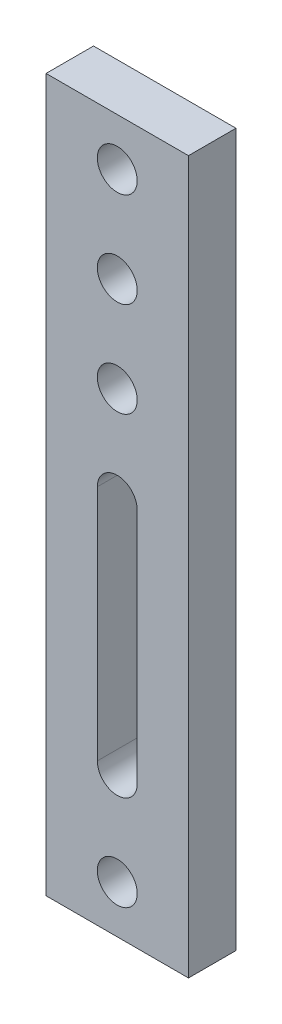
SolidWorks part; units mm, degrees
material "Простая углеродистая сталь"
ref_plane "Спереди" through (0, 0, 0) normal (0, 0, 1) x (1, 0, 0)
ref_plane "Сверху" through (0, 0, 0) normal (0, 1, 0) x (1, 0, 0)
ref_plane "Справа" through (0, 0, 0) normal (1, 0, 0) x (0, 0, -1)
sketch "Эскиз1" plane through (0, 0, 0) normal (0, 0, 1) x (1, 0, 0)
  line L1 (0, 0) -> (75, 0)
  line L2 (0, 0) -> (0, 375)
  line L3 (0, 375) -> (75, 375)
  line L4 (75, 0) -> (75, 375)
  dimension "D1" = 75
  dimension "D2" = 375
extrude "Бобышка-Вытянуть1" add sketch "Эскиз1" along normal blind 25
sketch "Эскиз2" plane through (0, 0, 25) normal (0, 0, 1) x (1, 0, 0)
  line L1 (27, 75) -> (27, 200)
  line L2 (48, 75) -> (48, 200)
  line L3 (0, 375) -> (0, 0) construction
  line L4 (0, 0) -> (75, 0) construction
  arc A0 (27, 75) -> (48, 75) centre (37.5, 75) ccw
  arc A1 (27, 200) -> (48, 200) centre (37.5, 200) cw
  circle A2 centre (37.5, 250) radius 10.5
  circle A3 centre (37.5, 300) radius 10.5
  circle A4 centre (37.5, 350) radius 10.5
  circle A5 centre (37.5, 25) radius 10.5
  point P7 (27, 137.5)
  point P10 (48, 137.5)
  dimension "D1" = 37.5
  dimension "D2" = 75
  dimension "D3" = 3
extrude "Вырез-Вытянуть1" cut sketch "Эскиз2" against normal through all
